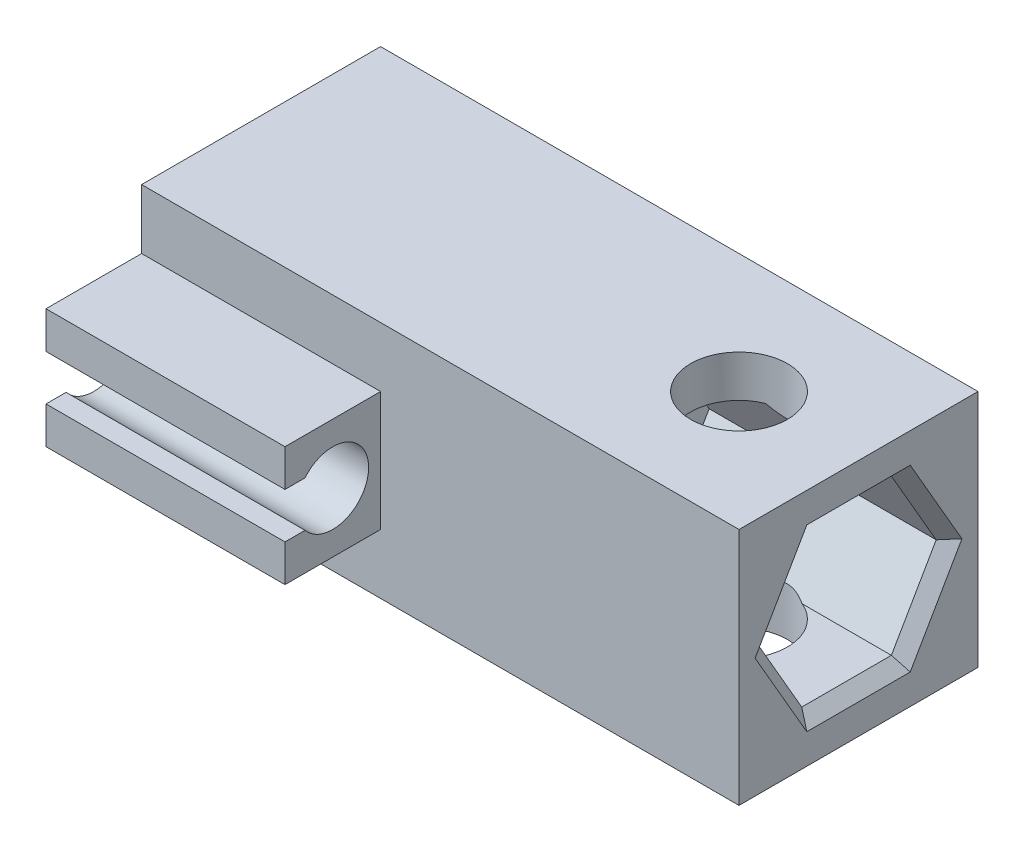
SolidWorks part; units mm, degrees
ref_plane "Спереди" through (0, 0, 0) normal (0, 0, 1) x (1, 0, 0)
ref_plane "Сверху" through (0, 0, 0) normal (0, 1, 0) x (1, 0, 0)
ref_plane "Справа" through (0, 0, 0) normal (1, 0, 0) x (0, 0, -1)
sketch "Sketch1" plane through (0, 0, 0) normal (0, 1, 0) x (1, 0, 0)
  line L0 (-25, 0) -> (25, 0) construction
  line L1 (25, -10) -> (-25, -10)
  line L2 (25, -10) -> (25, 10)
  line L3 (25, 10) -> (-25, 10)
  line L4 (-25, -10) -> (-25, 10)
  line L5 (25, -10) -> (-25, 10) construction
  line L6 (25, 10) -> (-25, -10) construction
  circle A0 centre (15, 0) radius 4.05
  point P0 (0, 0)
  dimension "D3" = 8.1
  dimension "D1" = 20
  dimension "D2" = 50
  dimension "D4" = 10
extrude "Boss-Extrude1" add sketch "Sketch1" along normal blind 20
sketch "Sketch2" plane through (-25, 0, 0) normal (-1, 0, 0) x (0, 0, 1)
  line L0 (0, 20) -> (0, 0) construction
  line L1 (-10, 20) -> (10, 20) construction
  line L2 (-10, 0) -> (10, 0) construction
  line L4 (5.05, 4.95) -> (-5.05, 4.95) construction
  line L5 (5.05, 4.95) -> (5.05, 15.05) construction
  line L6 (5.05, 15.05) -> (-5.05, 15.05) construction
  line L7 (-5.05, 4.95) -> (-5.05, 15.05) construction
  line L8 (5.05, 4.95) -> (-5.05, 15.05) construction
  line L9 (5.05, 15.05) -> (-5.05, 4.95) construction
  circle A0 centre (0, 10) radius 4.1
  point P6 (0, 10)
  dimension "D2" = 8.2
  dimension "D1" = 10.1
extrude "Cut-Extrude1" cut sketch "Sketch2" against normal through all
sketch "Sketch3" plane through (25, 0, 0) normal (1, 0, 0) x (0, 0, -1)
  line L0 (-10, 20) -> (10, 20) construction
  line L1 (-3.75, 16.4952) -> (-7.5, 10)
  line L2 (-7.5, 10) -> (-3.75, 3.5048)
  line L3 (-3.75, 3.5048) -> (3.75, 3.5048)
  line L4 (3.75, 3.5048) -> (7.5, 10)
  line L5 (7.5, 10) -> (3.75, 16.4952)
  line L6 (3.75, 16.4952) -> (-3.75, 16.4952)
  circle A0 centre (0, 10) radius 7.5 construction
  dimension "D1" = 15
extrude "Cut-Extrude2" cut sketch "Sketch3" against normal blind 20
sketch "Sketch8" plane through (-25, 0, 0) normal (-1, 0, 0) x (0, 0, 1)
  line L0 (10, 10) -> (18, 10) construction
  line L1 (10, 20) -> (10, 0) construction
  line L2 (18, 15) -> (18, 11.9)
  line L3 (18, 5) -> (10, 5)
  line L4 (18, 5) -> (18, 15) construction
  line L5 (18, 15) -> (10, 15)
  line L6 (10, 5) -> (10, 15)
  line L7 (18, 5) -> (10, 15) construction
  line L8 (18, 15) -> (10, 5) construction
  line L9 (18, 11.9) -> (16.3216, 11.9)
  line L10 (16.3216, 8.1) -> (18, 8.1)
  line L11 (18, 8.1) -> (18, 5)
  circle A0 centre (14, 10) radius 3 construction
  arc A1 (16.3216, 11.9) -> (16.3216, 8.1) centre (14, 10) ccw
  point P5 (14, 10)
  dimension "D1" = 6
  dimension "D2" = 3.8
  dimension "D3" = 8
  dimension "D4" = 10
extrude "Boss-Extrude3" add sketch "Sketch8" against normal blind 20
chamfer "Chamfer1" distance 1 angle 45 6 edges at (25, 13.2476, -5.625) (25, 6.7524, -5.625) (25, 3.5048, 0) (25, 6.7524, 5.625) (25, 13.2476, 5.625) (25, 16.4952, 0)
